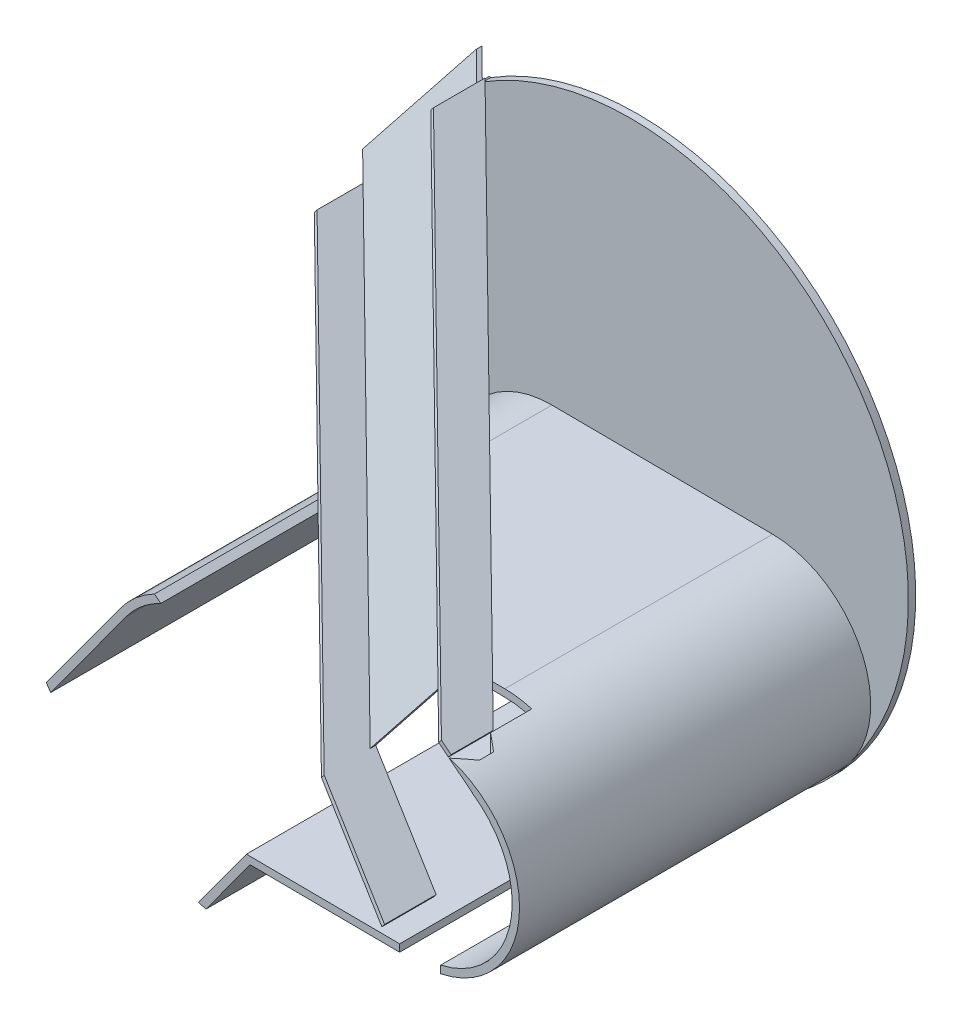
SolidWorks part; units mm, degrees
ref_plane "Front Plane" through (0, 0, 0) normal (0, 0, 1) x (1, 0, 0)
ref_plane "Top Plane" through (0, 0, 0) normal (0, 1, 0) x (1, 0, 0)
ref_plane "Right Plane" through (0, 0, 0) normal (1, 0, 0) x (0, 0, -1)
sketch "Sketch1" plane through (0, 0, 0) normal (0, 0, 1) x (1, 0, 0)
  line L0 (-46.7112, -11.734) -> (97.1223, -12.7005) construction
  line L1 (-22.4835, -136.8996) -> (96.2824, -137.6977) construction
  line L2 (-156.2216, -108.1426) -> (-104.6001, -37.3587)
  line L3 (-55.2262, -181.7968) -> (-3.6047, -111.0129)
  line L4 (-26.1122, -141.8754) -> (96.2488, -142.6975) construction
  line L5 (-100.5828, 161.1927) -> (115.5901, -10.3955) construction
  line L6 (-19.954, -141.9167) -> (-20.2698, -188.9157) construction
  line L7 (-178.9626, 63.8154) -> (102.7673, -159.8089) construction
  line L8 (-20.2698, -188.9157) -> (17.7293, -189.171) construction
  line L9 (96.7024, -75.1991) -> (158.6354, -83.5986) construction
  line L10 (-22.4835, -136.8996) -> (15.5156, -137.155) construction
  line L14 (-86.0705, -6.4712) -> (-87.5624, -21.3968) construction
  line L15 (-156.2227, 45.7655) -> (-81.5946, 38.3057) construction
  line L16 (-156.2227, 45.7655) -> (-162.1905, -13.937) construction
  line L17 (-162.1905, -13.937) -> (-87.5624, -21.3968) construction
  line L18 (-81.5946, 38.3057) -> (-83.0865, 23.3801) construction
  line L19 (-83.0865, 23.3801) -> (-23.3841, 17.4122) construction
  line L21 (-86.0705, -6.4712) -> (-26.368, -12.439) construction
  line L22 (-23.3841, 17.4122) -> (-26.368, -12.439) construction
  line L23 (-159.2066, 15.9143) -> (-24.876, 2.4866) construction
  line L24 (37.431, 77.7748) -> (25.2511, 86.5297) construction
  line L25 (117.7454, 112.41) -> (73.971, 51.5101) construction
  line L26 (117.7454, 112.41) -> (69.0255, 147.4296) construction
  line L27 (69.0255, 147.4296) -> (25.2511, 86.5297) construction
  line L28 (73.971, 51.5101) -> (61.791, 60.265) construction
  line L29 (61.791, 60.265) -> (26.7715, 11.5451) construction
  line L30 (37.431, 77.7748) -> (2.4115, 29.0549) construction
  line L31 (26.7715, 11.5451) -> (2.4115, 29.0549) construction
  line L32 (93.3855, 129.9198) -> (14.5915, 20.3) construction
  line L33 (48.6394, -71.3036) -> (62.3114, -65.1329) construction
  line L34 (38.4772, -158.1755) -> (7.6236, -89.8158) construction
  line L35 (38.4772, -158.1755) -> (93.165, -133.4926) construction
  line L36 (93.165, -133.4926) -> (62.3114, -65.1329) construction
  line L37 (7.6236, -89.8158) -> (21.2955, -83.6451) construction
  line L38 (21.2955, -83.6451) -> (-3.3874, -28.9573) construction
  line L39 (48.6394, -71.3036) -> (23.9565, -16.6158) construction
  line L40 (-3.3874, -28.9573) -> (23.9565, -16.6158) construction
  line L41 (65.8211, -145.8341) -> (10.2846, -22.7866) construction
  line L42 (10.2846, -22.7866) -> (0, 0) construction
  line L43 (14.5915, 20.3) -> (0, 0) construction
  line L44 (0, 0) -> (-24.876, 2.4866) construction
  line L45 (-178.9626, 63.8154) -> (-101.2491, 161.7216)
  line L46 (-101.2491, 161.7216) -> (-100.5828, 161.1927)
  line L47 (-46.7112, -11.734) -> (-46.6777, -6.7341) construction
  line L49 (-46.6777, -6.7341) -> (97.1559, -7.7006) construction
  line L50 (17.7293, -189.171) -> (18.0451, -142.1721) construction
  line L51 (18.0451, -142.1721) -> (-19.954, -141.9167) construction
  line L52 (-50.1137, -183.272) -> (-19.954, -141.9167) construction
  line L53 (86.606, 12.6107) -> (8.8926, -85.2954) construction
  arc A0 (-55.2262, -181.7968) -> (-100.5828, 161.1927) centre (0, 0) ccw
  arc A1 (-3.6047, -111.0129) -> (-104.6001, -37.3587) centre (-54.1024, -74.1858) ccw
  circle A2 centre (96.7024, -75.1991) radius 62.5 construction
  arc A3 (97.1559, -7.7006) -> (96.2488, -142.6975) centre (96.7024, -75.1991) cw construction
  arc A6 (-178.9626, 63.8154) -> (-156.2216, -108.1426) centre (0, 0) ccw
  dimension "D2" = 62.5
  dimension "D3" = 125
  dimension "D4" = 5
  dimension "D5" = 5
  dimension "D10" = 75
  dimension "D24" = 190
  dimension "D6" = 125
  dimension "D7" = 25
  dimension "D8" = 38
  dimension "D9" = 47
  dimension "D11" = 60
  dimension "D12" = 30
  dimension "D13" = 60
  dimension "D14" = 75
  dimension "D15" = 60
  dimension "D16" = 30
  dimension "D17" = 60
  dimension "D18" = 75
  dimension "D19" = 60
  dimension "D20" = 30
  dimension "D21" = 60
  dimension "D22" = 120
  dimension "D23" = 120
  dimension "D25" = 5
  dimension "D26" = 38
  dimension "D27" = 5
extrude "Boss-Extrude1" add sketch "Sketch1" along normal blind 5
sketch "Sketch2" plane through (0, 0, 5) normal (0, 0, 1) x (1, 0, 0)
  line L0 (-53.6825, -11.6872) -> (97.1223, -12.7005)
  line L1 (-22.4835, -136.8996) -> (96.2824, -137.6977)
  line L2 (-19.954, -141.9167) -> (96.2488, -142.6975)
  line L3 (-22.4835, -136.8996) -> (28.3946, -137.2415) construction
  line L5 (-53.6489, -6.6873) -> (97.1559, -7.7006)
  line L6 (-9.389, -115.2449) -> (-22.4835, -136.8996) construction
  line L7 (-26.1122, -141.8754) -> (96.2488, -142.6975) construction
  line L9 (-159.1887, -103.7255) -> (-108.6399, -34.4125)
  line L13 (-156.2216, -108.1426) -> (-104.6001, -37.3587) construction
  line L14 (-104.6001, -37.3587) -> (-156.2216, -108.1426)
  line L15 (-50.1137, -183.272) -> (-19.954, -141.9167)
  line L16 (-55.2262, -181.7968) -> (-22.4835, -136.8996)
  line L17 (-55.2262, -181.7968) -> (-50.1137, -183.272)
  line L18 (-55.2262, -181.7968) -> (-3.6047, -111.0129) construction
  line L19 (-46.6777, -6.7341) -> (97.1559, -7.7006) construction
  arc A0 (96.2824, -137.6977) -> (97.1223, -12.7005) centre (96.7024, -75.1991) ccw
  arc A1 (97.1559, -7.7006) -> (96.2488, -142.6975) centre (96.7024, -75.1991) cw
  arc A2 (-3.6047, -111.0129) -> (-104.6001, -37.3587) centre (-54.1024, -74.1858) ccw construction
  arc A3 (-55.2262, -181.7968) -> (-100.5828, 161.1927) centre (0, 0) ccw construction
  arc A4 (-178.9626, 63.8154) -> (-156.2216, -108.1426) centre (0, 0) ccw construction
  arc A5 (-53.6489, -6.6873) -> (-108.6399, -34.4125) centre (-54.1024, -74.1858) ccw
  arc A6 (-53.6825, -11.6872) -> (-104.6001, -37.3587) centre (-54.1024, -74.1858) ccw
  arc A7 (-159.1887, -103.7255) -> (-156.2216, -108.1426) centre (0, 0) ccw
  arc A8 (96.2488, -142.6975) -> (97.1559, -7.7006) centre (96.7024, -75.1991) ccw construction
  arc A10 (-3.6047, -111.0129) -> (-104.6001, -37.3587) centre (-54.1024, -74.1858) ccw construction
  dimension "D3" = 5
  dimension "D5" = 125
  dimension "D9" = 5
  dimension "D6" = 5
  dimension "D1" = 59.224
  dimension "D2" = 5
  dimension "D4" = 5
  dimension "D10" = 5
extrude "Boss-Extrude2" add sketch "Sketch2" along normal blind 240
ref_plane "Plane1" through (-38.0976, -47.9967, 0) normal (-0.6217, -0.7832, 0) x (0.7832, -0.6217, 0)
ref_plane "Plane2" through (39.6158, 49.9094, 0) normal (-0.6217, -0.7832, 0) x (0.7832, -0.6217, 0)
ref_plane "Plane4" through (-46.875, 37.2072, 0) normal (-0.7832, 0.6217, 0) x (0, 0, 1)
sketch "Sketch3" plane through (0, 0, 245) normal (0, 0, 1) x (1, 0, 0)
  line L0 (-46.6777, -6.7341) -> (97.1559, -7.7006) construction
  line L6 (-22.3286, -18.4774) -> (115.7783, -19.4054)
  line L7 (-53.6489, -6.6873) -> (97.1559, -7.7006)
  line L8 (115.5901, -10.3955) -> (132.5435, -23.8523)
  line L9 (-100.5828, 161.1927) -> (115.5901, -10.3955) construction
  line L10 (-178.9626, 63.8154) -> (102.7673, -159.8089) construction
  line L11 (-77.1643, -16.9874) -> (-22.3286, -18.4774)
  line L14 (-152.0857, 202.0733) -> (231.3173, -102.2545) construction
  line L17 (-82.3425, -12.8772) -> (-77.1643, -16.9874)
  arc A0 (96.2488, -142.6975) -> (97.1559, -7.7006) centre (96.7024, -75.1991) ccw construction
  arc A1 (-53.6489, -6.6873) -> (-108.6399, -34.4125) centre (-54.1024, -74.1858) ccw construction
  arc A2 (97.1559, -7.7006) -> (115.5901, -10.3955) centre (96.7024, -75.1991) cw
  arc A5 (-53.6489, -6.6873) -> (-82.3425, -12.8772) centre (-54.1024, -74.1858) ccw
  arc A6 (-53.6489, -6.6873) -> (-108.6399, -34.4125) centre (-54.1024, -74.1858) ccw construction
  arc A9 (115.7783, -19.4054) -> (132.5435, -23.8523) centre (115.5451, -54.1105) cw
extrude "Cut-Extrude1" cut sketch "Sketch3" against normal blind 57
sketch "Sketch5" plane through (-0.9208, -137.0445, 0) normal (0.0067, 1, 0) x (1, -0.0067, 0)
  line L0 (97.2055, -245) -> (-21.5632, -245) construction
  line L1 (83.2068, -5) -> (111.2068, -5)
  line L2 (83.2068, -5) -> (83.2068, -245)
  line L3 (83.2068, -245) -> (111.2068, -245)
  line L4 (111.2068, -5) -> (111.2068, -245)
  line L5 (-21.5632, -245) -> (-21.5632, -5) construction
  line L7 (97.2055, -5) -> (-53.6027, -5) construction
  dimension "D1" = 104.77
  dimension "D2" = 28
  dimension "D3" = 0
extrude "Cut-Extrude2" cut sketch "Sketch5" against normal blind 10 and the other way blind 2
sketch "Sketch6" plane through (0, 0, 5) normal (0, 0, 1) x (1, 0, 0)
  line L0 (96.7024, -75.1991) -> (96.2488, -142.6975) construction
  line L1 (-26.1122, -141.8754) -> (96.2488, -142.6975) construction
  arc A0 (96.2488, -142.6975) -> (97.1559, -7.7006) centre (96.7024, -75.1991) ccw construction
sketch "Sketch8" plane through (39.6158, 49.9094, 0) normal (-0.6217, -0.7832, 0) x (0.7832, -0.6217, 0)
  line L0 (-179.8468, 5) -> (59.9939, 188)
  line L1 (59.9939, 188) -> (59.9939, 0) construction
  line L2 (80.8848, 188) -> (-37.8629, 188) construction
  line L3 (59.9939, 188) -> (59.9939, 223.2197) construction
  line L4 (59.9939, 223.2197) -> (-179.8468, 40.2197)
  line L5 (-179.8468, 40.2197) -> (-179.8468, 5)
  line L7 (96.9988, 245) -> (96.9988, 216.235)
  line L8 (96.9988, 216.235) -> (59.9939, 188)
  line L10 (59.9939, 223.2197) -> (88.5393, 245)
  line L12 (96.9988, 188) -> (96.9988, 245) construction
  line L13 (96.9988, 245) -> (88.5393, 245)
  line L14 (118.6438, 245) -> (96.9988, 245) construction
  dimension "D1" = 28
extrude "Boss-Extrude3" add sketch "Sketch8" against normal blind 3 separate body
sketch "Sketch9" plane through (39.6158, 49.9094, 0) normal (0.6217, 0.7832, 0) x (-0.7832, 0.6217, 0)
  line L1 (-59.9939, 191.7735) -> (-59.9939, 188)
  line L5 (-59.9939, 188) -> (194.4326, -6.129)
  line L6 (179.8468, 5) -> (-96.9988, 216.235) construction
  line L8 (194.4326, -6.129) -> (194.4326, -2.3555)
  line L9 (178.9962, 0) -> (-96.9988, 0) construction
  line L10 (194.4326, -2.3555) -> (-59.9939, 191.7735)
  point P1 (179.8468, 8.7735)
  point P7 (0, 0)
  point P8 (0, 0)
  point P11 (0, 0)
  point P12 (179.8468, 8.7735)
  point P14 (0, 0)
  point P15 (0, 0)
  dimension "D1" = 3
extrude "Boss-Extrude8" add sketch "Sketch9" against normal blind 125 separate body
sketch "Sketch11" plane through (-38.0976, -47.9967, 0) normal (-0.6217, -0.7832, 0) x (0.7832, -0.6217, 0)
  line L0 (-179.8468, 5) -> (-179.8468, 40.2197)
  line L1 (-179.8468, 40.2197) -> (59.9939, 223.2197)
  line L2 (59.9939, 223.2197) -> (59.9939, 188) construction
  line L3 (88.5393, 245) -> (-179.8468, 40.2197) construction
  line L4 (-179.8468, 5) -> (96.9988, 216.235) construction
  line L5 (59.9939, 188) -> (-179.8468, 5)
  line L6 (59.9939, 188) -> (-194.4326, -6.129) construction
  line L7 (59.9939, 0) -> (59.9939, 188) construction
  line L9 (59.9939, 223.2197) -> (137.6239, 242.704)
  line L10 (137.6239, 242.704) -> (137.6239, 207.4843)
  line L11 (137.6239, 207.4843) -> (59.9939, 188)
  point P18 (0, 0)
  point P19 (0, 0)
extrude "Boss-Extrude9" add sketch "Sketch11" along normal blind 3 separate body
sketch "Sketch12" plane through (-53.7213, 42.6415, 89.8914) normal (0.4751, -0.3771, -0.795) x (-0.8799, -0.2036, -0.4293)
  line L0 (-206.8837, -112.2739) -> (64.8773, 159.0581)
  line L1 (64.8773, 159.0581) -> (157.4351, 66.354)
  line L3 (157.4351, 66.354) -> (-136.196, -226.8135)
  line L4 (-136.196, -226.8135) -> (-206.8837, -112.2739)
  line L5 (144.4518, 53.3912) -> (-69.0387, -159.7623) construction
  line L6 (155.3154, 68.477) -> (66.9969, 156.9352) construction
  point P10 (0, 0)
  point P11 (0, 0)
  point P13 (-194.0736, -105.5495)
  point P14 (0, 0)
extrude "Cut-Extrude3" cut sketch "Sketch12" against normal blind 150
